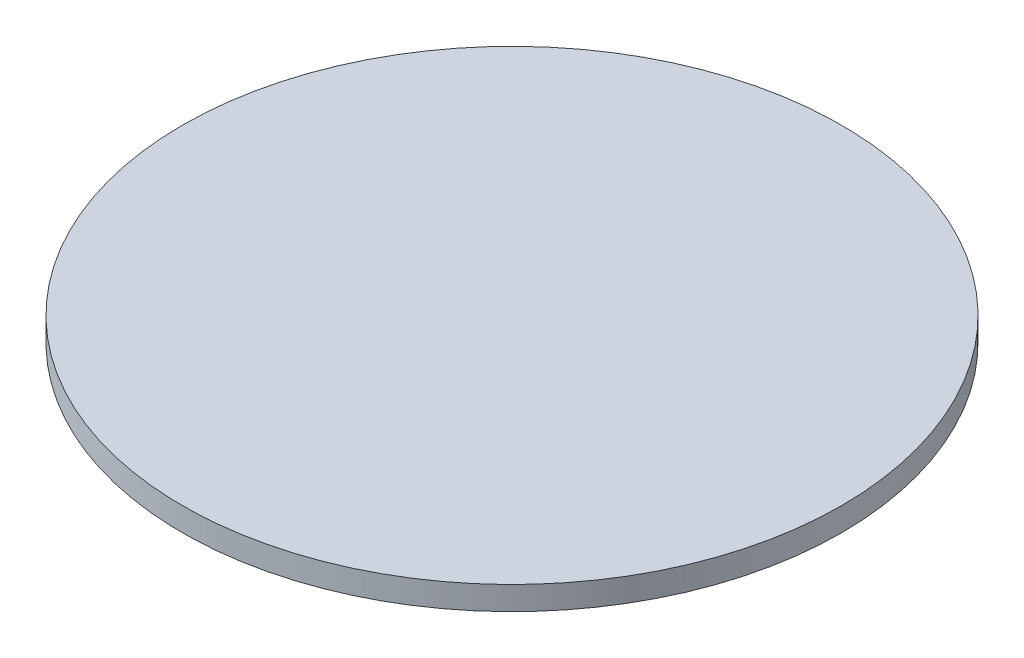
SolidWorks part; units mm, degrees
ref_plane "Front Plane" through (0, 0, 0) normal (0, 0, 1) x (1, 0, 0)
ref_plane "Top Plane" through (0, 0, 0) normal (0, 1, 0) x (1, 0, 0)
ref_plane "Right Plane" through (0, 0, 0) normal (1, 0, 0) x (0, 0, -1)
sketch "Sketch1" plane through (0, 0, 0) normal (0, 0, 1) x (1, 0, 0)
  line L0 (0, 1) -> (14, 1)
  line L1 (14, 1) -> (14, 0)
  line L2 (14, 0) -> (13.5, 0)
  line L3 (13.5, 0) -> (13.5, 0.7)
  line L4 (13.5, 0.7) -> (0, 0.7)
  line L5 (0, 0.7) -> (0, 1)
  line L6 (0, 0) -> (0, 1.691) construction
  dimension "D1" = 0.3
  dimension "D2" = 0.5
  dimension "D3" = 14
  dimension "D4" = 1
revolve "Revolve1" add sketch "Sketch1" angle 360 about L6
